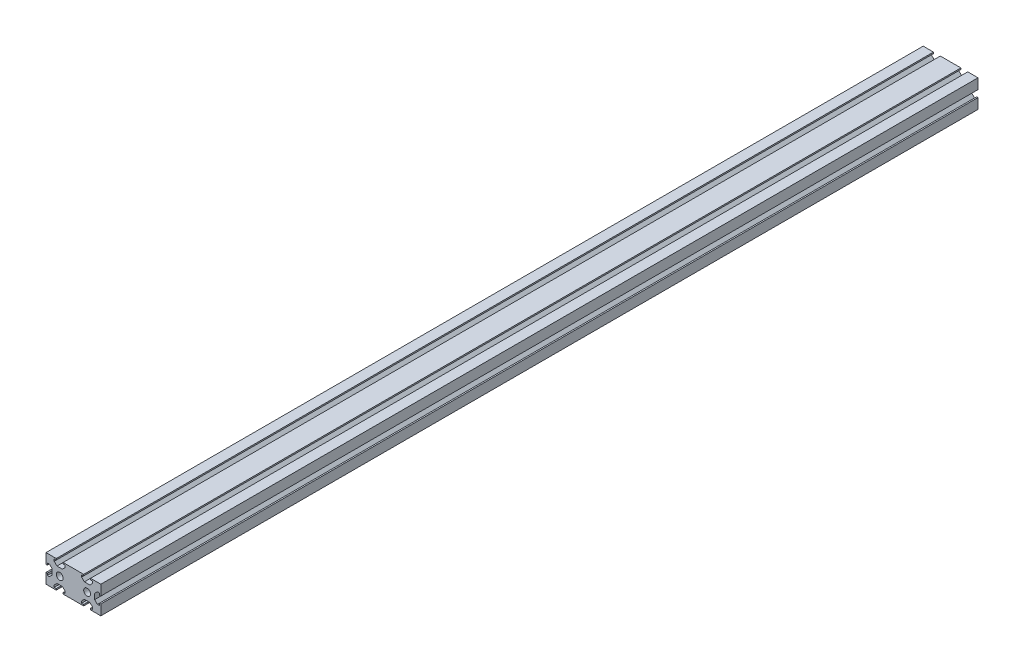
SolidWorks part; units mm, degrees
ref_plane "前视基准面" through (0, 0, 0) normal (0, 0, 1) x (1, 0, 0)
ref_plane "上视基准面" through (0, 0, 0) normal (0, 1, 0) x (1, 0, 0)
ref_plane "右视基准面" through (0, 0, 0) normal (1, 0, 0) x (0, 0, -1)
sketch "草图1" plane through (0, 0, 0) normal (0, 0, 1) x (1, 0, 0)
  line L1 (20, -10) -> (-20, -10)
  line L2 (20, -10) -> (20, 10)
  line L3 (20, 10) -> (-20, 10)
  line L4 (-20, -10) -> (-20, 10)
  line L5 (20, -10) -> (-20, 10) construction
  line L6 (20, 10) -> (-20, -10) construction
  point P0 (0, 0)
  dimension "D1" = 40
  dimension "D2" = 20
extrude "凸台-拉伸1" add sketch "草图1" along normal mid plane 640
sketch "草图2" plane through (0, 0, -320) normal (0, 0, -1) x (-1, 0, 0)
  line L0 (0, 10) -> (0, -10) construction
  line L1 (-20, 10) -> (20, 10) construction
  line L2 (20, -10) -> (-20, -10) construction
  line L3 (-20, 0) -> (20, 0) construction
  line L4 (-20, -10) -> (-20, 10) construction
  line L5 (20, 10) -> (20, -10) construction
  line L6 (-12.5, 10) -> (-12.5, 9)
  line L7 (-12.5, 9) -> (-14, 9)
  line L8 (-14, 9) -> (-14, 7.5)
  line L9 (-14, 7.5) -> (-12, 5.5)
  line L10 (-12, 5.5) -> (-8, 5.5)
  line L11 (-8, 5.5) -> (-6, 7.5)
  line L12 (-6, 7.5) -> (-6, 9)
  line L13 (-6, 9) -> (-7.5, 9)
  line L14 (-7.5, 9) -> (-7.5, 10)
  line L15 (-7.5, 10) -> (-12.5, 10)
  line L16 (-7.5, -9) -> (-7.5, -10)
  line L17 (-6, -9) -> (-7.5, -9)
  line L18 (-6, -7.5) -> (-6, -9)
  line L19 (-8, -5.5) -> (-6, -7.5)
  line L20 (-12, -5.5) -> (-8, -5.5)
  line L21 (-14, -7.5) -> (-12, -5.5)
  line L22 (-14, -9) -> (-14, -7.5)
  line L23 (-12.5, -9) -> (-14, -9)
  line L24 (-12.5, -10) -> (-12.5, -9)
  line L25 (-7.5, -10) -> (-12.5, -10)
  line L26 (-20, 2.5) -> (-19, 2.5)
  line L27 (-19, 2.5) -> (-19, 4)
  line L28 (-19, 4) -> (-17.5, 4)
  line L29 (-17.5, 4) -> (-15.5, 2)
  line L30 (-15.5, 2) -> (-15.5, -2)
  line L31 (-15.5, -2) -> (-17.5, -4)
  line L32 (-17.5, -4) -> (-19, -4)
  line L33 (-19, -4) -> (-19, -2.5)
  line L34 (-19, -2.5) -> (-20, -2.5)
  line L35 (-20, -2.5) -> (-20, 2.5)
  line L36 (7.5, 9) -> (7.5, 10)
  line L37 (6, 9) -> (7.5, 9)
  line L38 (6, 7.5) -> (6, 9)
  line L39 (8, 5.5) -> (6, 7.5)
  line L40 (12, 5.5) -> (8, 5.5)
  line L41 (14, 7.5) -> (12, 5.5)
  line L42 (14, 9) -> (14, 7.5)
  line L43 (12.5, 9) -> (14, 9)
  line L44 (12.5, 10) -> (12.5, 9)
  line L45 (7.5, 10) -> (12.5, 10)
  line L46 (6, -9) -> (7.5, -9)
  line L47 (6, -7.5) -> (6, -9)
  line L48 (8, -5.5) -> (6, -7.5)
  line L49 (12, -5.5) -> (8, -5.5)
  line L50 (14, -7.5) -> (12, -5.5)
  line L51 (14, -9) -> (14, -7.5)
  line L52 (12.5, -9) -> (14, -9)
  line L53 (12.5, -10) -> (12.5, -9)
  line L54 (7.5, -10) -> (12.5, -10)
  line L55 (7.5, -9) -> (7.5, -10)
  line L56 (19, -2.5) -> (20, -2.5)
  line L57 (19, -4) -> (19, -2.5)
  line L58 (17.5, -4) -> (19, -4)
  line L59 (15.5, -2) -> (17.5, -4)
  line L60 (15.5, 2) -> (15.5, -2)
  line L61 (17.5, 4) -> (15.5, 2)
  line L62 (19, 4) -> (17.5, 4)
  line L63 (19, 2.5) -> (19, 4)
  line L64 (20, 2.5) -> (19, 2.5)
  line L65 (20, -2.5) -> (20, 2.5)
  circle A0 centre (-10, 0) radius 2.5
  circle A2 centre (10, 0) radius 2.5
  point P20 (-10, 10)
  point P43 (-20, 0)
  point P76 (0, 0)
  dimension "D9" = 5
  dimension "D1" = 20
  dimension "D2" = 8
  dimension "D3" = 4.5
  dimension "D4" = 5
  dimension "D5" = 1
  dimension "D6" = 1.5
  dimension "D7" = 4
  dimension "D8" = 4.5
extrude "切除-拉伸1" cut sketch "草图2" against normal through all
